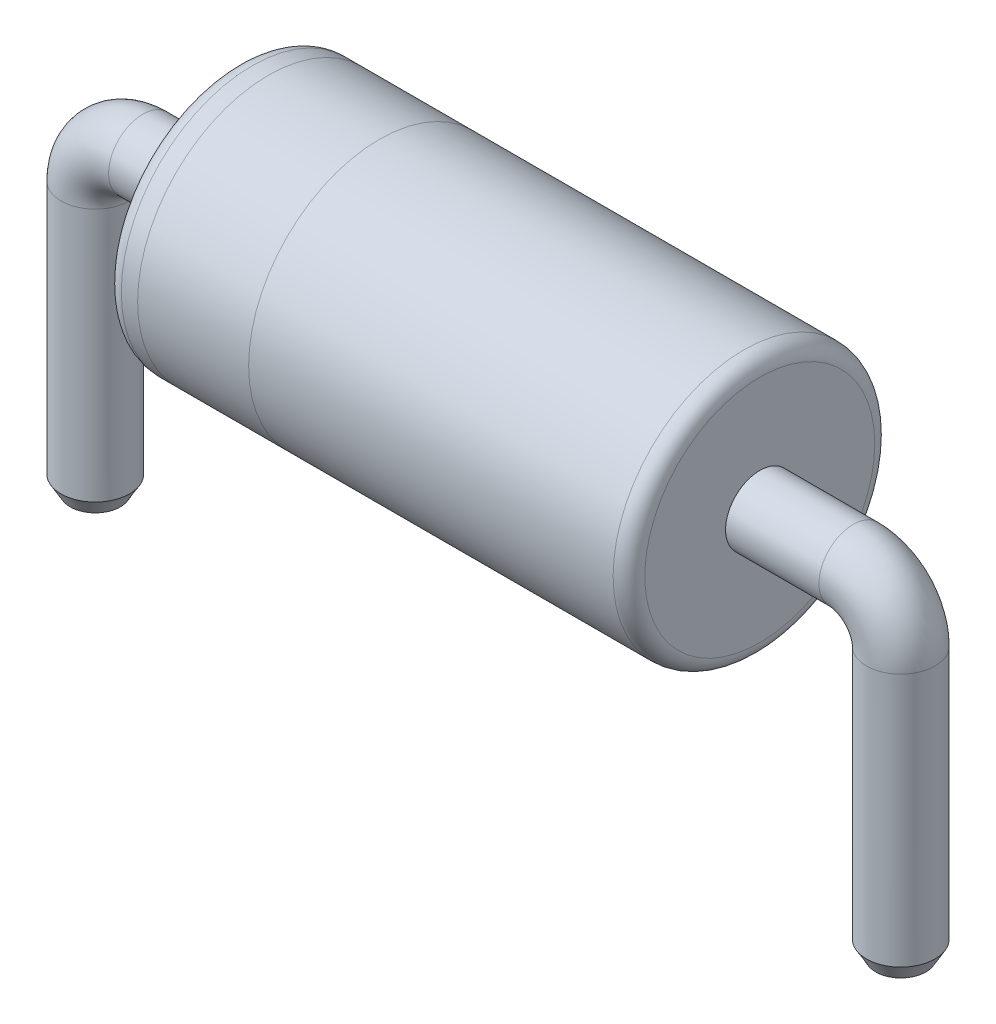
SolidWorks part; units mm, degrees
ref_plane "Front Plane" through (0, 0, 0) normal (0, 0, 1) x (1, 0, 0)
ref_plane "Top Plane" through (0, 0, 0) normal (0, 1, 0) x (1, 0, 0)
ref_plane "Right Plane" through (0, 0, 0) normal (1, 0, 0) x (0, 0, -1)
sketch "Sketch1" plane through (0, 0, 0) normal (0, 1, 0) x (1, 0, 0)
  circle A0 centre (0, 0) radius 0.2159
  dimension "D1" = 0.4318
sketch "Sketch2" plane through (0, 0, 0) normal (0, 0, 1) x (1, 0, 0)
  line L0 (0, 0) -> (0, 1.7)
  line L1 (-0.3, 2) -> (-4.78, 2)
  line L2 (-5.08, 1.7) -> (-5.08, 0)
  line L3 (0.2159, 0) -> (-0.2159, 0) construction
  arc A0 (-4.78, 2) -> (-5.08, 1.7) centre (-4.78, 1.7) ccw
  arc A1 (-0.3, 2) -> (0, 1.7) centre (-0.3, 1.7) cw
  point P8 (0, 2)
  point P11 (-5.08, 2)
  dimension "D1" = 0.3
  dimension "D2" = 2
  dimension "D3" = 5.08
sweep "Sweep1" add profiles "Sketch1" path "Sketch2"
sketch3d "3DSketch2" plane through (0, 0, 0) normal (0, 0, 1) x (1, 0, 0)
  dimension "D1" = 0.889
sketch "Sketch3" plane through (-0.889, 0, 0) normal (1, 0, 0) x (0, 0, -1)
  circle A0 centre (0, 2) radius 0.825
  dimension "D1" = 1.65
extrude "Extrude1" add sketch "Sketch3" against normal blind 3.302
fillet "Fillet1" radius 0.1 2 edges at (-4.191, 2, -0.825) (-0.889, 2, -0.825)
chamfer "Chamfer1" distance 0.1 angle 30 2 edges at (-5.08, 0, 0.2159) (0, 0, 0.2159)
sketch3d "3DSketch3" plane through (0, 0, 0) normal (0, 0, 1) x (1, 0, 0)
  dimension "D1" = 2
sketch "Sketch4" plane through (0, 0, 2) normal (0, 0, 1) x (1, 0, 0)
  line L1 (-3.2879, 2.9006) -> (-3.9879, 2.9006)
  line L2 (-3.2879, 2.9006) -> (-3.2879, 1.0788)
  line L3 (-3.2879, 1.0788) -> (-3.9879, 1.0788)
  line L4 (-3.9879, 2.9006) -> (-3.9879, 1.0788)
  dimension "D1" = 0.7
split line "Split Line1"
